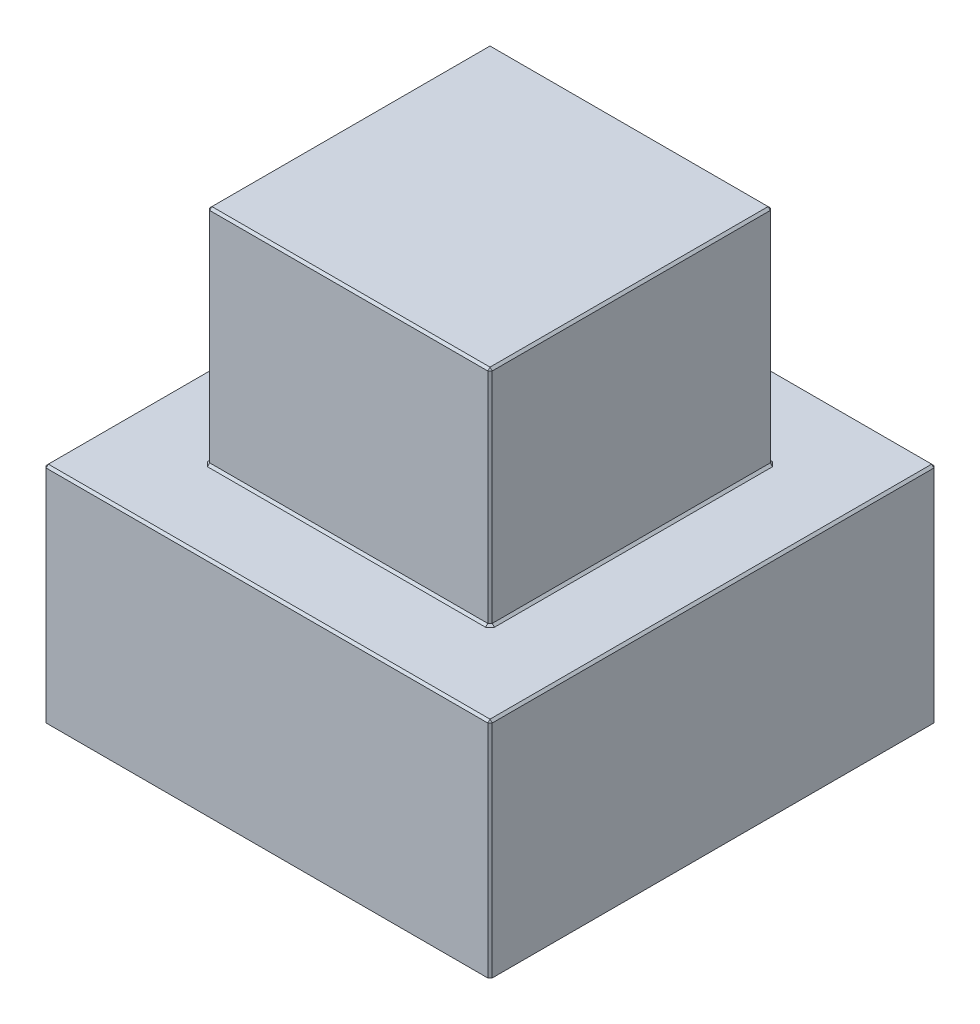
SolidWorks part; units mm, degrees
ref_plane "Plan de face" through (0, 0, 0) normal (0, 0, 1) x (1, 0, 0)
ref_plane "Plan de dessus" through (0, 0, 0) normal (0, 1, 0) x (1, 0, 0)
ref_plane "Plan de droite" through (0, 0, 0) normal (1, 0, 0) x (0, 0, -1)
sketch "Esquisse1" plane through (0, 0, 0) normal (0, 1, 0) x (1, 0, 0)
  line L1 (-3, -3) -> (3, -3)
  line L2 (-3, -3) -> (-3, 3)
  line L3 (-3, 3) -> (3, 3)
  line L4 (3, -3) -> (3, 3)
  line L5 (-3, -3) -> (3, 3) construction
  line L6 (-3, 3) -> (3, -3) construction
  point P0 (0, 0)
  dimension "D1" = 6
extrude "Boss.-Extru.1" add sketch "Esquisse1" along normal blind 3
sketch "Esquisse2" plane through (0, 3, 0) normal (0, 1, 0) x (1, 0, 0)
  line L1 (-1.9, -1.9) -> (1.9, -1.9)
  line L2 (-1.9, -1.9) -> (-1.9, 1.9)
  line L3 (-1.9, 1.9) -> (1.9, 1.9)
  line L4 (1.9, -1.9) -> (1.9, 1.9)
  line L5 (-1.9, -1.9) -> (1.9, 1.9) construction
  line L6 (-1.9, 1.9) -> (1.9, -1.9) construction
  point P0 (0, 0)
  dimension "D1" = 3.8
extrude "Boss.-Extru.2" add sketch "Esquisse2" along normal blind 3
chamfer "Chanfrein1" distance 0.03 angle 45 22 edges at (1.9, 4.5, -1.9) (0, 6, -1.9) (-1.9, 4.5, -1.9) (0, 3, -1.9) (1.9, 3, 0) (-1.9, 3, 0) (0, 3, 1.9) (1.9, 6, 0) (-1.9, 6, 0) (0, 6, 1.9) (1.9, 4.5, 1.9) (3, 0, 0) (0, 0, -3) (3, 3, 0) (3, 1.5, 3) (0, 3, 3) (-3, 3, 0) (-3, 1.5, -3) (0, 3, -3) (3, 1.5, -3) (-1.9, 4.5, 1.9) (-3, 1.5, 3)
